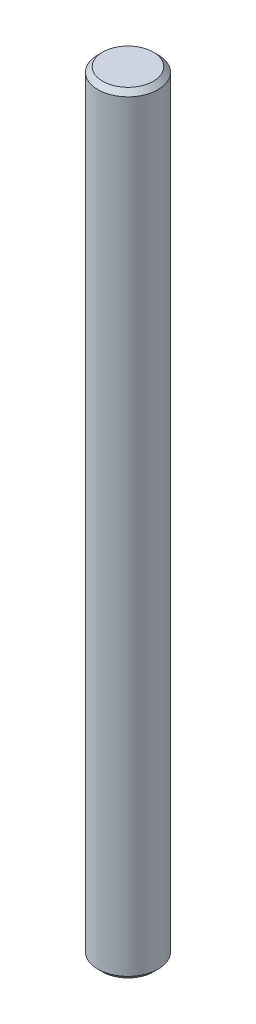
SolidWorks part; units mm, degrees
ref_plane "Top" through (0, 0, 0) normal (0, 0, 1) x (1, 0, 0)
ref_plane "Front" through (0, 0, 0) normal (0, 1, 0) x (1, 0, 0)
ref_plane "Right" through (0, 0, 0) normal (1, 0, 0) x (0, 0, -1)
sketch "Sketch1" plane through (0, 0, 0) normal (0, 1, 0) x (1, 0, 0)
  circle A0 centre (0, 0) radius 0.7937
  dimension "D1" = 1.5875
extrude "Extrude1" add sketch "Sketch1" along normal mid plane 20.32
chamfer "Chamfer1" distance 0.127 angle 45 2 edges at (0, -10.16, 0.7937) (0, 10.16, 0.7937)
